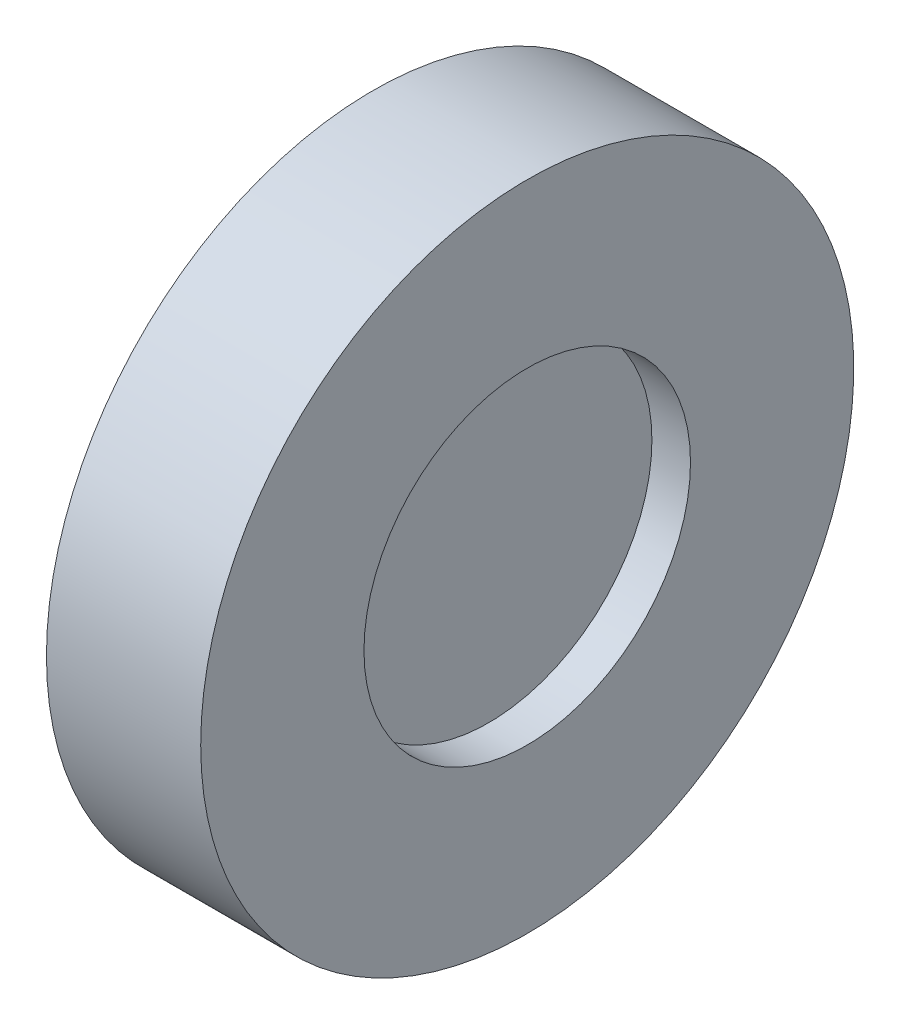
SolidWorks part; units mm, degrees
ref_plane "前视基准面" through (0, 0, 0) normal (0, 0, 1) x (1, 0, 0)
ref_plane "上视基准面" through (0, 0, 0) normal (0, 1, 0) x (1, 0, 0)
ref_plane "右视基准面" through (0, 0, 0) normal (1, 0, 0) x (0, 0, -1)
sketch "草图1" plane through (0, 0, 0) normal (0, 0, 1) x (1, 0, 0)
  line L0 (-1.5, 6.35) -> (-1.5, 0)
  line L2 (-1.5, 6.35) -> (1.5, 6.35)
  line L3 (-1.5, 0) -> (1.5, 0)
  line L4 (1.5, 6.35) -> (1.5, 0)
revolve "旋转2" add sketch "草图1" angle 360 about L3
sketch "草图4" plane through (0, 0, 0) normal (0, 0, 1) x (1, 0, 0)
  line L0 (-3, 12.7) -> (3, 12.7)
  line L1 (3, 12.7) -> (3, 6.35)
  line L2 (3, 6.35) -> (-3, 6.35)
  line L3 (1.5, 6.35) -> (-1.5, 6.35) construction
  line L4 (-3, 6.35) -> (-3, 12.7)
  line L5 (0, 6.35) -> (0, 12.7) construction
  line L6 (-1.6142, 0) -> (1.5903, 0) construction
revolve "旋转3" add sketch "草图4" angle 360 about L6
equation "\"D1@草图4\"=\"D1@草图1\""
